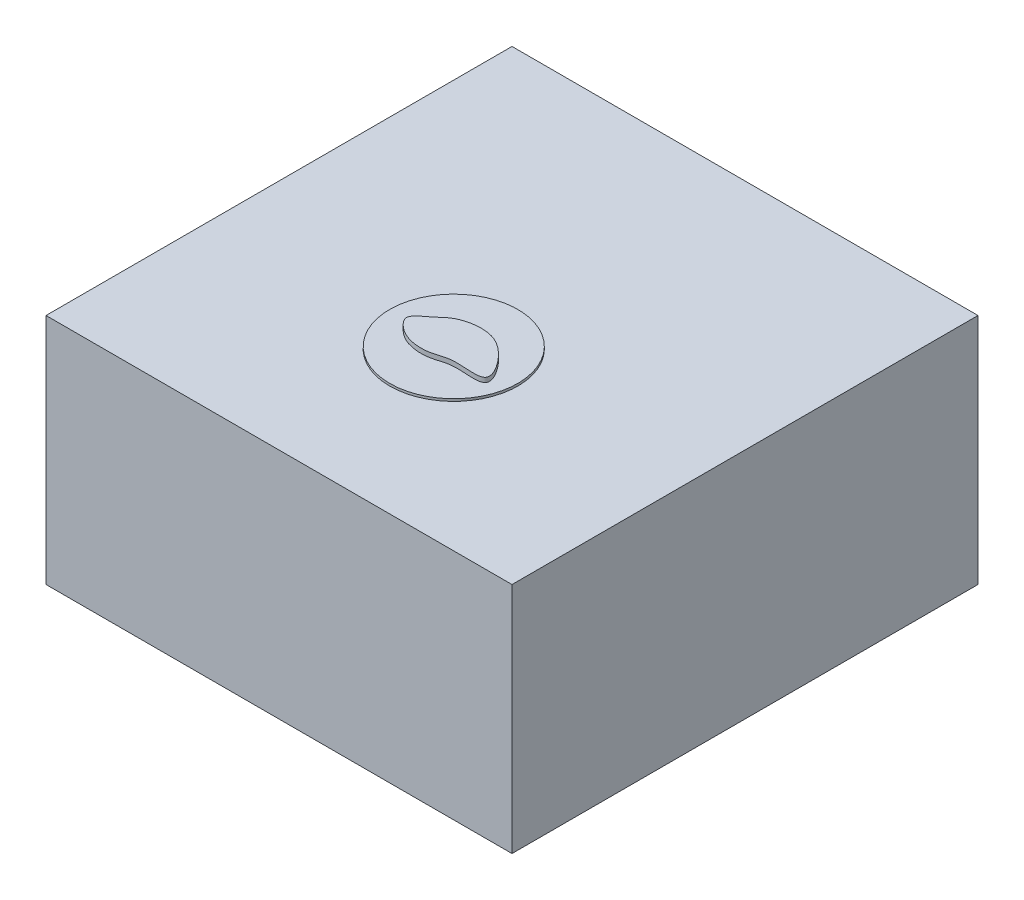
SolidWorks part; units mm, degrees
ref_plane "Front Plane" through (0, 0, 0) normal (0, 0, 1) x (1, 0, 0)
ref_plane "Top Plane" through (0, 0, 0) normal (0, 1, 0) x (1, 0, 0)
ref_plane "Right Plane" through (0, 0, 0) normal (1, 0, 0) x (0, 0, -1)
sketch "Sketch1" plane through (0, 0, 0) normal (0, 0, 1) x (1, 0, 0)
  line L1 (-10, -5) -> (10, -5)
  line L2 (-10, -5) -> (-10, 5)
  line L3 (-10, 5) -> (10, 5)
  line L4 (10, -5) -> (10, 5)
  line L5 (0, 5) -> (0, -5) construction
  line L6 (-10, 0) -> (10, 0) construction
  point P0 (0, 0)
  dimension "D1" = 20
  dimension "D2" = 10
extrude "Boss-Extrude1" add sketch "Sketch1" along normal blind 20
sketch "Sketch2" plane through (0, 0, 20) normal (0, 0, 1) x (1, 0, 0)
  line L0 (-10, -5) -> (10, -5) construction
  line L1 (0, 0) -> (0, -5) construction
  line L3 (10, 5) -> (-10, 5) construction
  circle A0 centre (-7.5, 4) radius 0.5
  circle A1 centre (7.5, 4) radius 0.5
  dimension "D1" = 1
  dimension "D2" = 7.5
  dimension "D3" = 1
ref_plane "Plane1" through (7.5, 0, 0) normal (1, 0, 0) x (0, 0, -1)
sketch "Sketch3" plane through (7.5, 0, 0) normal (1, 0, 0) x (0, 0, -1)
  line L3 (-20, 4) -> (-5, 4)
  line L4 (-20, 4.5) -> (-20, 3.5) construction
  line L5 (-20, 5) -> (0, 5) construction
  arc A0 (-5, 4) -> (-4, 5) centre (-5, 5) ccw
  dimension "D1" = 1
  dimension "D2" = 15
sweep "ag/agcl electrodes" add profiles "Sketch2" path "Sketch3"
sketch "Sketch5" plane through (0, 5, 0) normal (0, 1, 0) x (1, 0, 0)
  line L0 (0, -12.5) -> (2.75, -12.5) construction
  line L2 (0, -12.5) -> (0, -9.75) construction
  line L3 (-10, -20) -> (-10, 0) construction
  line L5 (10, -20) -> (-10, -20) construction
  circle A0 centre (0, -12.5) radius 2.75
  dimension "D1" = 5.5
  dimension "D2" = 10
  dimension "D3" = 7.5
extrude "Boss-Extrude4" add sketch "Sketch5" along normal blind 0.1 separate body
sketch "Sketch8" plane through (0, 5.1, 0) normal (0, -1, 0) x (-1, 0, 0)
  line L0 (0, -12.5) -> (2.75, -12.5) construction
  line L2 (0, -12.5) -> (0, -9.75) construction
  circle A1 centre (0, -12.5) radius 0.005
  circle A2 centre (0.5, -12.5) radius 0.005
  circle A3 centre (0.5, -12) radius 0.005
  circle A4 centre (0, -12) radius 0.005
  circle A5 centre (0.5, -13) radius 0.005
  circle A6 centre (0, -13) radius 0.005
  circle A7 centre (-0.5, -13) radius 0.005
  circle A8 centre (-0.5, -12) radius 0.005
  circle A9 centre (-0.5, -12.5) radius 0.005
  circle A10 centre (0, -12.5) radius 2.75 construction
  dimension "D1" = 0.5
  dimension "D2" = 0.01
  dimension "D5" = 0.5
  dimension "D3" = 2
  dimension "D4" = 2
extrude "Boss-Extrude5" add sketch "Sketch8" along normal blind 0.1 separate body
sketch "Sketch4" plane through (0, 5, 0) normal (0, 1, 0) x (1, 0, 0)
  line L0 (0, -11.4373) -> (0, -13.4201) construction
  line L1 (-2.0803, -12.5) -> (1.6023, -12.5) construction
  spline S0 degree 3 poles (-2.0861, -12.5392) (-1.3776, -12.1296) (-0.8241, -11.549) (0.2513, -11.3226) (1.3726, -11.7466) (2.6529, -13.5718) (0.7805, -13.1045) (-0.1221, -13.5063) (-0.9948, -13.461) (-1.5864, -13.1169) (-2.0861, -12.5392) (-1.3776, -12.1296) (-0.8241, -11.549) knots -0.204834 -0.133435 -0.089031 0 0.049563 0.182818 0.303261 0.461561 0.613381 0.684438 0.795166 0.866565 0.910969 1 1.049563 1.182818 1.303261 only from (-1.3298, -12.0471) to (-1.3298, -12.0471)
extrude "slice" add sketch "Sketch4" along normal blind 0.3 separate body
